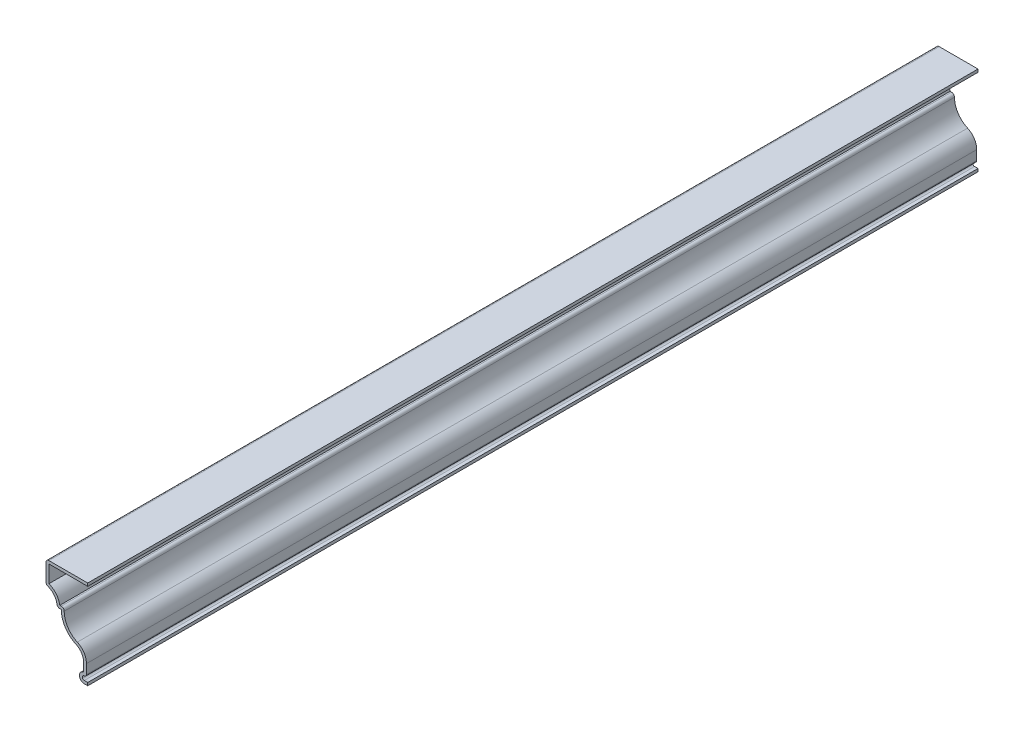
SolidWorks part; units mm, degrees
ref_plane "Front Plane" through (0, 0, 0) normal (0, 0, 1) x (1, 0, 0)
ref_plane "Top Plane" through (0, 0, 0) normal (0, 1, 0) x (1, 0, 0)
ref_plane "Right Plane" through (0, 0, 0) normal (1, 0, 0) x (0, 0, -1)
sketch "Sketch1" plane through (0, 0, 0) normal (0, 0, 1) x (1, 0, 0)
  line L0 (0, 0) -> (0, 59.6894) construction
  line L1 (0, 0) -> (-1.9691, 0)
  line L2 (-2.3813, 5.5562) -> (-2.3812, 10.5905)
  line L3 (-15.0813, 30.1625) -> (-17.4625, 30.1625)
  line L4 (0, 50.8) -> (-23.8125, 50.8)
  line L5 (-23.8125, 50.8) -> (-23.8125, 38.1)
  line L6 (-1.9691, 1.651) -> (0, 1.651)
  line L7 (-0.7303, 5.1747) -> (-0.7303, 10.5905)
  line L8 (-13.3219, 31.8135) -> (-15.9265, 31.8135)
  line L9 (-22.1615, 49.149) -> (-22.1615, 39.3482)
  line L10 (0, 49.149) -> (-22.1615, 49.149)
  line L11 (-0.7303, 1.651) -> (-0.7303, 10.5905) construction
  line L12 (0, 1.651) -> (0, 0)
  line L13 (0, 1.651) -> (-0.7303, 1.651) construction
  line L14 (0, 50.8) -> (0, 49.149)
  arc A0 (-1.9691, 0) -> (-2.3813, 5.5562) centre (-1.9691, 2.7934) cw
  arc A1 (-2.3812, 10.5905) -> (-6.6146, 17.1145) centre (-9.525, 10.5905) ccw
  arc A2 (-6.6146, 17.1145) -> (-15.0813, 30.1625) centre (-0.7938, 30.1625) cw
  arc A3 (-23.8125, 38.1) -> (-17.4625, 30.1625) centre (-25.3984, 30.3225) cw
  arc A4 (-1.9691, 3.9358) -> (-1.9691, 1.651) centre (-1.9691, 2.7934) ccw
  arc A5 (-0.7303, 10.5905) -> (-5.942, 18.6223) centre (-9.525, 10.5905) ccw
  arc A6 (-5.942, 18.6223) -> (-13.3219, 31.8135) centre (-0.7938, 30.1625) cw
  arc A7 (-22.1615, 39.3482) -> (-15.9265, 31.8135) centre (-25.3984, 30.3225) cw
  arc A8 (-0.7303, 1.651) -> (-0.7303, 1.651) centre (-0.7303, 1.651) cw construction
  arc A9 (-1.9691, 3.9358) -> (-0.7303, 5.1747) centre (-1.9691, 5.1747) ccw
  dimension "D4" = 7.9375
  dimension "D7" = 14.2875
  dimension "D8" = 7.1437
  dimension "D13" = 2.3813
  dimension "D16" = 1.651
  dimension "D1" = 50.8
  dimension "D2" = 12.7
  dimension "D3" = 7.9375
  dimension "D5" = 24.6062
  dimension "D6" = 2.3813
  dimension "D9" = 6.35
  dimension "D10" = 10.3187
  dimension "D11" = 4.7625
  dimension "D12" = 23.8125
  dimension "D14" = 5.5562
  dimension "D15" = 1.651
extrude "Boss-Extrude1" add sketch "Sketch1" against normal blind 508
fillet "Fillet1" radius 1.651 4 edges at (-23.8125, 50.8, -254) (-23.8125, 38.1, -254) (-17.4625, 30.1625, -254) (-13.3219, 31.8135, -254)
